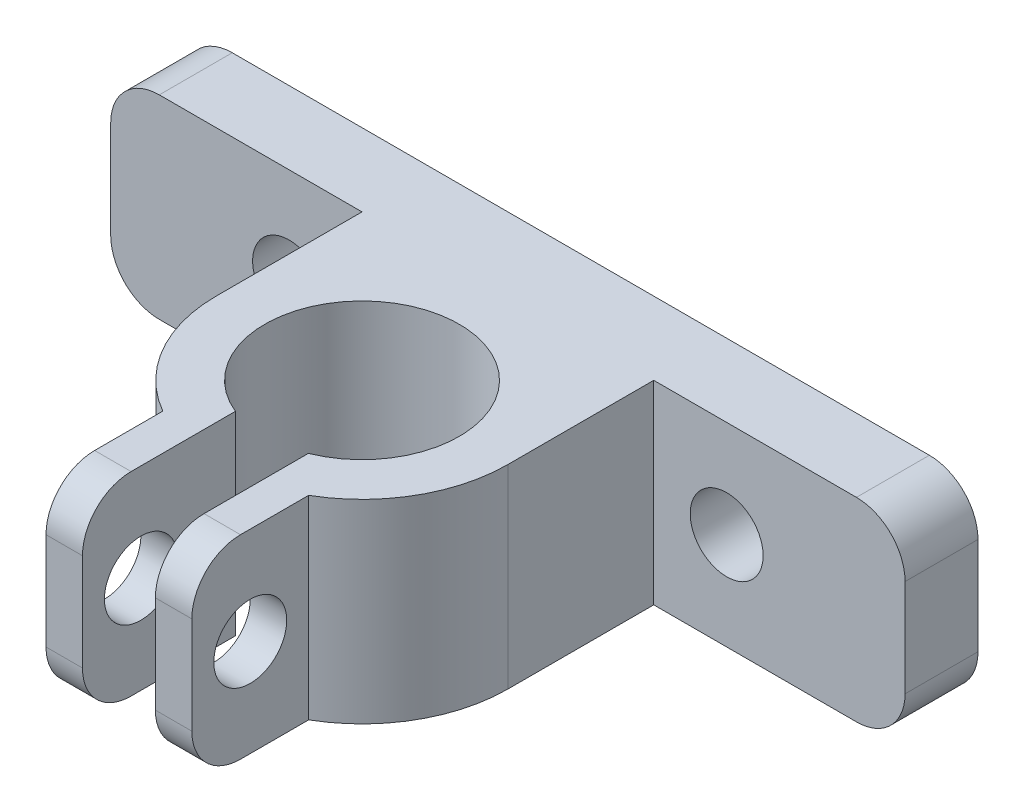
SolidWorks part; units mm, degrees
ref_plane "前视基准面" through (0, 0, 0) normal (0, 0, 1) x (1, 0, 0)
ref_plane "上视基准面" through (0, 0, 0) normal (0, 1, 0) x (1, 0, 0)
ref_plane "右视基准面" through (0, 0, 0) normal (1, 0, 0) x (0, 0, -1)
sketch "草图1" plane through (0, 0, 0) normal (0, 0, 1) x (1, 0, 0)
  line L0 (12.612, 26.3586) -> (-20.0654, 26.3586) construction
  line L2 (-20.0654, 30.3586) -> (12.612, 30.3586)
  line L3 (-20.0654, 30.3586) -> (-20.0654, 22.3586)
  line L4 (-20.0654, 22.3586) -> (12.612, 22.3586)
  line L5 (12.612, 30.3586) -> (12.612, 22.3586)
  line L6 (-20.0654, 30.3586) -> (12.612, 22.3586) construction
  line L7 (-20.0654, 22.3586) -> (12.612, 30.3586) construction
  point P4 (-3.7267, 26.3586)
extrude "凸台-拉伸1" add sketch "草图1" against normal blind 3
sketch "草图2" plane through (0, 0, 0) normal (0, 0, 1) x (1, 0, 0)
  line L0 (-3.7267, 30.3586) -> (-3.7267, 22.3586) construction
  line L3 (12.612, 30.3586) -> (-20.0654, 30.3586) construction
  line L4 (-20.0654, 22.3586) -> (12.612, 22.3586) construction
  line L5 (-3.7267, 26.3586) -> (5.2733, 26.3586) construction
  line L6 (-3.7267, 26.3586) -> (-12.7267, 26.3586) construction
  circle A2 centre (-12.7267, 26.3586) radius 1.5
  circle A3 centre (5.2733, 26.3586) radius 1.5
extrude "切除-拉伸1" cut sketch "草图2" against normal through all
sketch "草图3" plane through (0, 22.3586, 0) normal (0, -1, 0) x (1, 0, 0)
  line L0 (-20.0654, 0) -> (12.612, 0) construction
  line L1 (-3.7267, 0) -> (-3.7267, 6) construction
  circle A0 centre (-3.7267, 6) radius 6
  point P0 (-3.7267, 0)
extrude "凸台-拉伸2" add sketch "草图3" against normal up to surface (8 mm away) separate body up to face at (-3.7267, 30.3586, -1.5)
sketch "草图4" plane through (0, 22.3586, 0) normal (0, -1, 0) x (1, 0, 0)
  circle A0 centre (-3.7267, 6) radius 4
extrude "切除-拉伸2" cut sketch "草图4" against normal through all
sketch "草图5" plane through (0, 22.3586, 0) normal (0, -1, 0) x (1, 0, 0)
  line L0 (-9.7267, 6) -> (-9.7267, 0)
  line L1 (-20.0654, 0) -> (12.612, 0) construction
  line L2 (-9.7267, 0) -> (-3.7267, 0)
  line L3 (-3.7267, 0) -> (-9.7267, 6)
  line L4 (-3.7267, 0) -> (2.2733, 6)
  line L5 (2.2733, 6) -> (2.2733, 0)
  line L6 (2.2733, 0) -> (-3.7267, 0)
  circle A0 centre (-3.7267, 6) radius 6 construction
  point P8 (2.2733, 6)
extrude "凸台-拉伸3" add sketch "草图5" against normal up to surface (8 mm away) contours L3 L0 L2 | L4 L5 L6 up to face at (-3.7267, 30.3586, 2)
sketch "草图6" plane through (0, 22.3586, 0) normal (0, -1, 0) x (1, 0, 0)
  line L0 (-3.7267, 10) -> (2.2733, 10) construction
  line L2 (-0.7267, 10) -> (-6.7267, 10)
  line L3 (-0.7267, 10) -> (-0.7267, 16)
  line L4 (-0.7267, 16) -> (-6.7267, 16)
  line L5 (-6.7267, 10) -> (-6.7267, 16)
  circle A0 centre (-3.7267, 6) radius 4 construction
extrude "凸台-拉伸4" add sketch "草图6" against normal up to surface (8 mm away) up to face at (-3.7267, 30.3586, 1.5)
sketch "草图8" plane through (0, 22.3586, 0) normal (0, -1, 0) x (1, 0, 0)
  line L0 (0.2733, 6) -> (-7.7267, 6) construction
  line L2 (-2.2267, 6) -> (-5.2267, 6)
  line L3 (-2.2267, 6) -> (-2.2267, 16.4666)
  line L4 (-2.2267, 16.4666) -> (-5.2267, 16.4666)
  line L5 (-5.2267, 6) -> (-5.2267, 16.4666)
  circle A1 centre (-3.7267, 6) radius 4 construction
  point P8 (-3.7267, 6)
  point P9 (-3.7267, 6)
extrude "切除-拉伸5" cut sketch "草图8" against normal through all
sketch "草图9" plane through (-0.7267, 0, 0) normal (1, 0, 0) x (0, 0, -1)
  line L0 (-13.5981, 30.3586) -> (-13.5981, 24.9373) construction
  line L1 (-11.1962, 30.3586) -> (-16, 30.3586) construction
  line L2 (-16, 26.3586) -> (-11.1962, 26.3586) construction
  line L3 (-16, 30.3586) -> (-16, 22.3586) construction
  line L4 (-11.1962, 22.3586) -> (-11.1962, 30.3586) construction
  circle A0 centre (-13.5981, 26.3586) radius 1.5
extrude "切除-拉伸6" cut sketch "草图9" against normal through all
fillet "圆角1" radius 2 4 edges at (12.612, 22.3586, -1.5) (12.612, 30.3586, -1.5) (-20.0654, 22.3586, -1.5) (-20.0654, 30.3586, -1.5)
fillet "圆角2" radius 2 4 edges at (-5.9767, 30.3586, 16) (-5.9767, 22.3586, 16) (-1.4767, 22.3586, 16) (-1.4767, 30.3586, 16)
